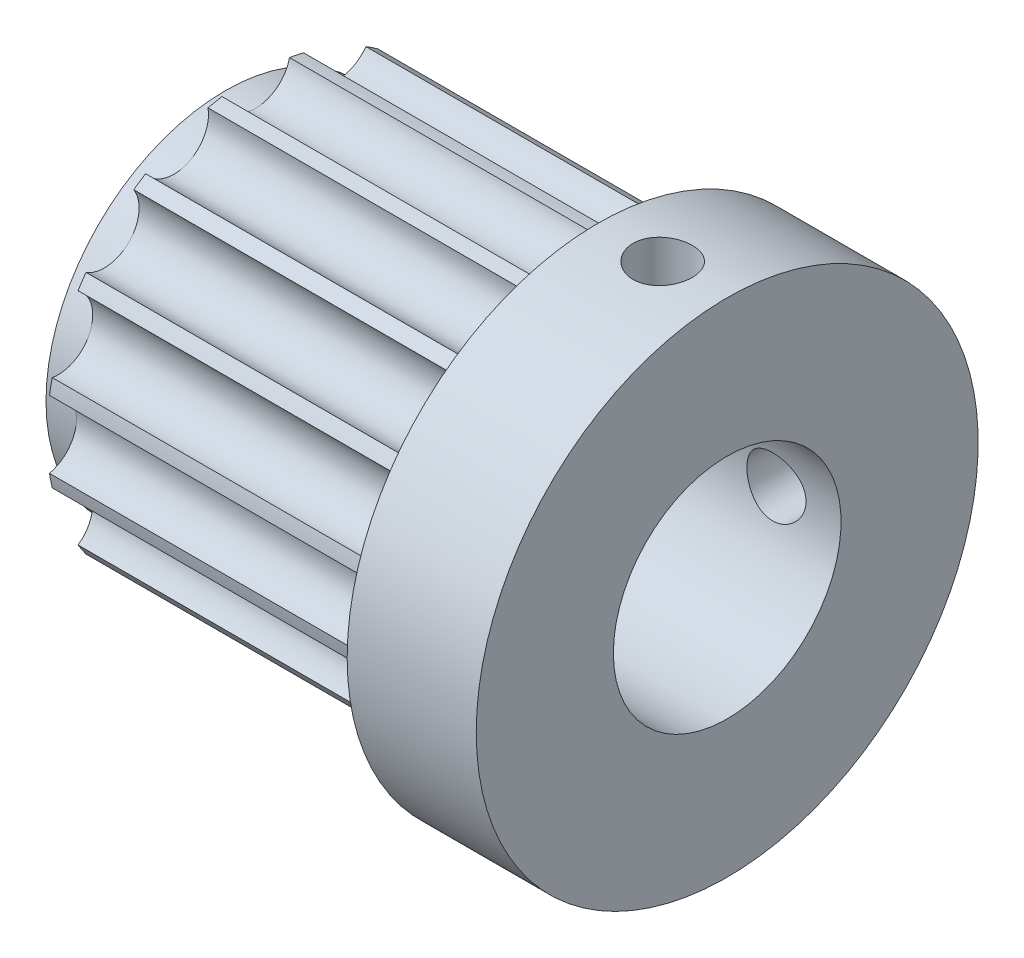
SolidWorks part; units mm, degrees
ref_plane "Front" through (0, 0, 0) normal (0, 0, 1) x (1, 0, 0)
ref_plane "Top" through (0, 0, 0) normal (0, 1, 0) x (1, 0, 0)
ref_plane "Right" through (0, 0, 0) normal (1, 0, 0) x (0, 0, -1)
sketch "Sketch1" plane through (0, 0, 0) normal (0, 0, 1) x (1, 0, 0)
  line L0 (0, 0) -> (64.6735, 0) construction
  line L1 (-11.25, 6.35) -> (16.75, 6.35)
  line L2 (16.75, 6.35) -> (16.75, 14)
  line L3 (9.55, 14) -> (16.75, 14)
  line L6 (9.55, 14) -> (9.55, 11.66)
  line L7 (9.55, 11.66) -> (-9.55, 11.66)
  line L8 (-9.55, 11.66) -> (-9.55, 10)
  line L9 (-11.25, 10) -> (-9.55, 10)
  line L10 (-9.55, 10) -> (-9.5232, 9.9814)
  line L12 (-11.25, 10) -> (-11.25, 6.35)
  point P4 (0, 11.66)
  dimension "D1" = 28
  dimension "D2" = 19.1
  dimension "D3" = 1.7
  dimension "D4" = 20
  dimension "D5" = 23.32
  dimension "D6" = 7.2
  dimension "D7" = 12.7
revolve "Revolve1" add sketch "Sketch1" angle 360 about L0
sketch "Sketch2" plane through (-9.55, 0, 0) normal (-1, 0, 0) x (0, 0, 1)
  circle A0 centre (0, 11.93) radius 1.93
  circle A3 centre (0, 0) radius 10 construction
  dimension "D1" = 3.86
extrude "Cut-Extrude1" cut sketch "Sketch2" against normal up to surface (19.1 mm away) up to face at (9.55, 0, 11.66)
pattern_circular "CirPattern1" count 16 over 360 about axis through (0, 0, 0) along (1, 0, 0) of "Cut-Extrude1"
hole_wizard "M4x0.7 Tapped Hole1" positions "Sketch4" profile "Sketch3" tap size "M4x0.7" standard "ANSI Metric"
sketch "Sketch4" plane through (0, 0, 0) normal (0, 1, 0) x (1, 0, 0)
  line L0 (9.55, 0) -> (16.75, 0) construction
  line L1 (9.55, 1.8831) -> (9.55, -1.8831) construction
  line L2 (16.75, -14) -> (16.75, 14) construction
  point P0 (13.15, 0)
sketch "Sketch3" plane through (13.15, 0, 0) normal (1, 0, 0) x (0, 0, -1)
  line L0 (0, 0) -> (0, 14.001)
  line L1 (0, 14.001) -> (1.65, 14.001)
  line L2 (1.65, 14.001) -> (1.65, 0)
  line L5 (1.65, 0) -> (0, 0)
  line L11 (0, -6.35) -> (0, 107.95) construction
  dimension "Thru Tap Drill Dia." = 3.3
  dimension "Thru Tap Drill Depth" = 14.001
cosmetic thread "Hole Thread1" parameters "D2"=4
pattern_circular "CirPattern2" count 2 over 90 about axis through (0, 0, 0) along (-1, 0, 0) of "M4x0.7 Tapped Hole1"
